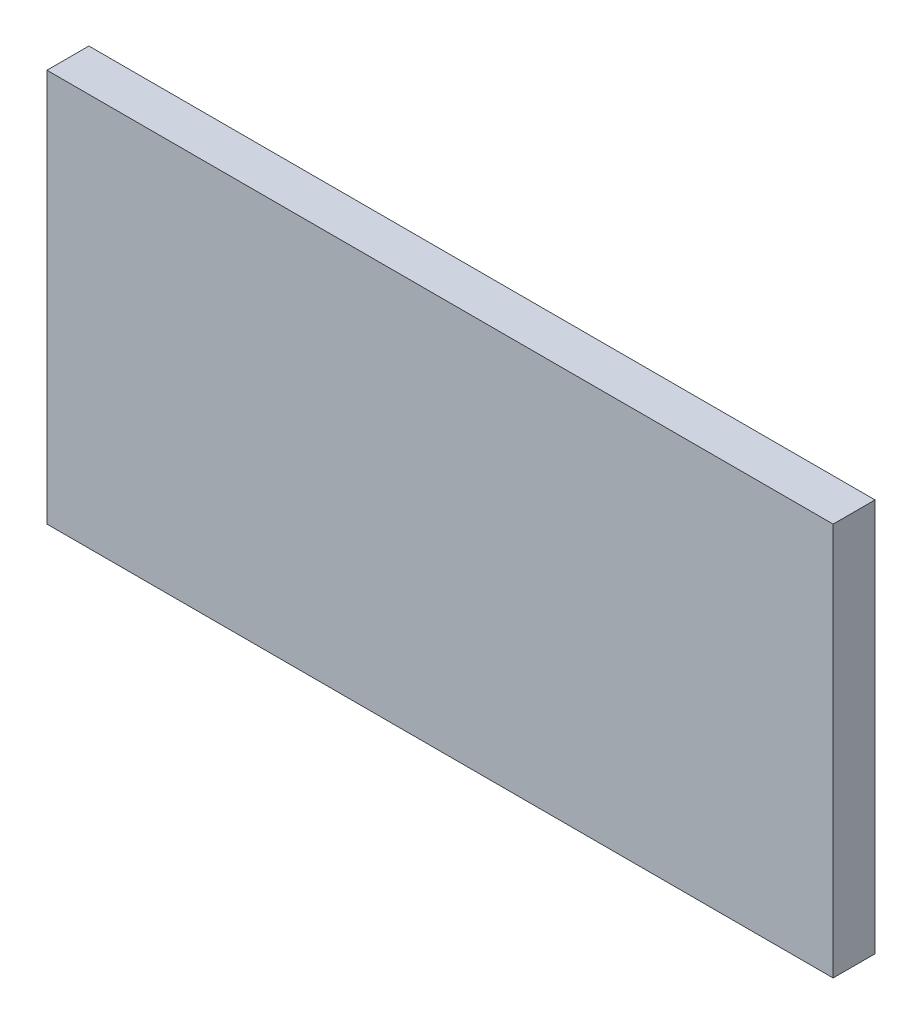
SolidWorks part; units mm, degrees
ref_plane "Front Plane" through (0, 0, 0) normal (0, 0, 1) x (1, 0, 0)
ref_plane "Top Plane" through (0, 0, 0) normal (0, 1, 0) x (1, 0, 0)
ref_plane "Right Plane" through (0, 0, 0) normal (1, 0, 0) x (0, 0, -1)
sketch "Sketch1" plane through (0, 0, 0) normal (0, 0, 1) x (1, 0, 0)
  line L1 (15, 7.5) -> (-15, 7.5)
  line L2 (15, 7.5) -> (15, -7.5)
  line L3 (15, -7.5) -> (-15, -7.5)
  line L4 (-15, 7.5) -> (-15, -7.5)
  line L5 (15, 7.5) -> (-15, -7.5) construction
  line L6 (15, -7.5) -> (-15, 7.5) construction
  point P0 (0, 0)
  dimension "D1" = 15
  dimension "D2" = 30
extrude "Boss-Extrude1" add sketch "Sketch1" along normal blind 1.6
